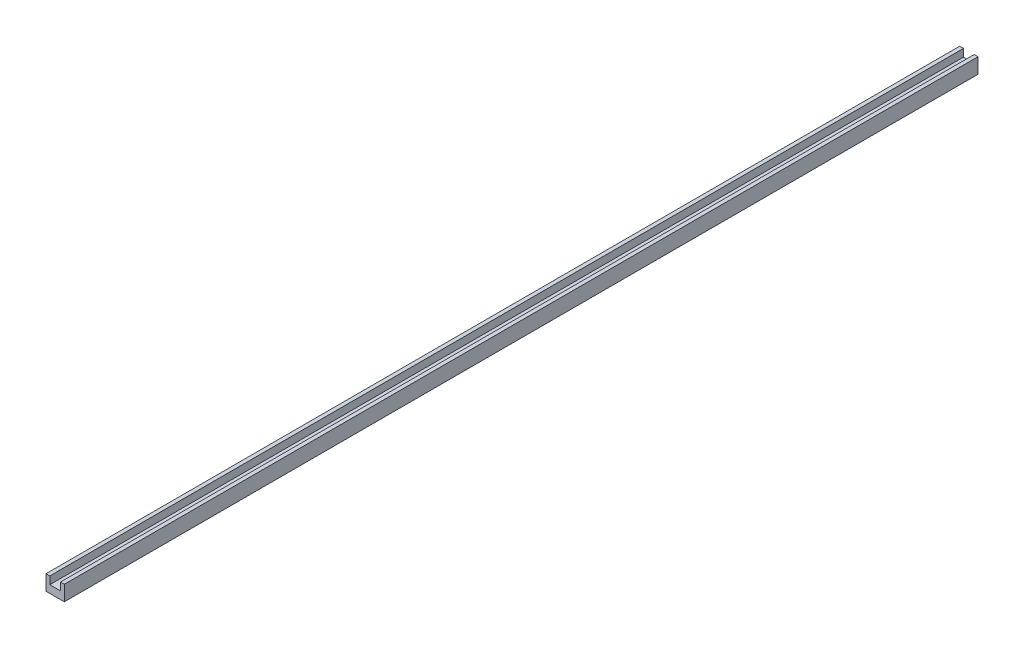
SolidWorks part; units mm, degrees
ref_plane "Front Plane" through (0, 0, 0) normal (0, 0, 1) x (1, 0, 0)
ref_plane "Top Plane" through (0, 0, 0) normal (0, 1, 0) x (1, 0, 0)
ref_plane "Right Plane" through (0, 0, 0) normal (1, 0, 0) x (0, 0, -1)
sketch "Sketch2" plane through (0, 0, 0) normal (0, 0, 1) x (1, 0, 0)
  line L1 (0, 0) -> (12, 0)
  line L2 (0, 0) -> (0, 10)
  line L3 (0, 10) -> (12, 10)
  line L4 (12, 0) -> (12, 10)
  dimension "D1" = 12
  dimension "D2" = 10
extrude "Boss-Extrude1" add sketch "Sketch2" along normal blind 600
sketch "Sketch4" plane through (0, 0, 600) normal (0, 0, 1) x (1, 0, 0)
  line L0 (12, 10) -> (0, 10) construction
  line L1 (2.5, 10) -> (9.5, 10)
  line L2 (2.5, 10) -> (2.5, 5)
  line L3 (2.5, 5) -> (9.5, 5)
  line L4 (9.5, 10) -> (9.5, 5)
  line L6 (2.5, 10) -> (0, 10)
  line L7 (9.5, 10) -> (12, 10)
  line M10 (12, 10) -> (0, 10)
  dimension "D1" = 7
  dimension "D2" = 5
extrude "Cut-Extrude1" cut sketch "Sketch4" against normal through all contours L4 L2 L3 M10
